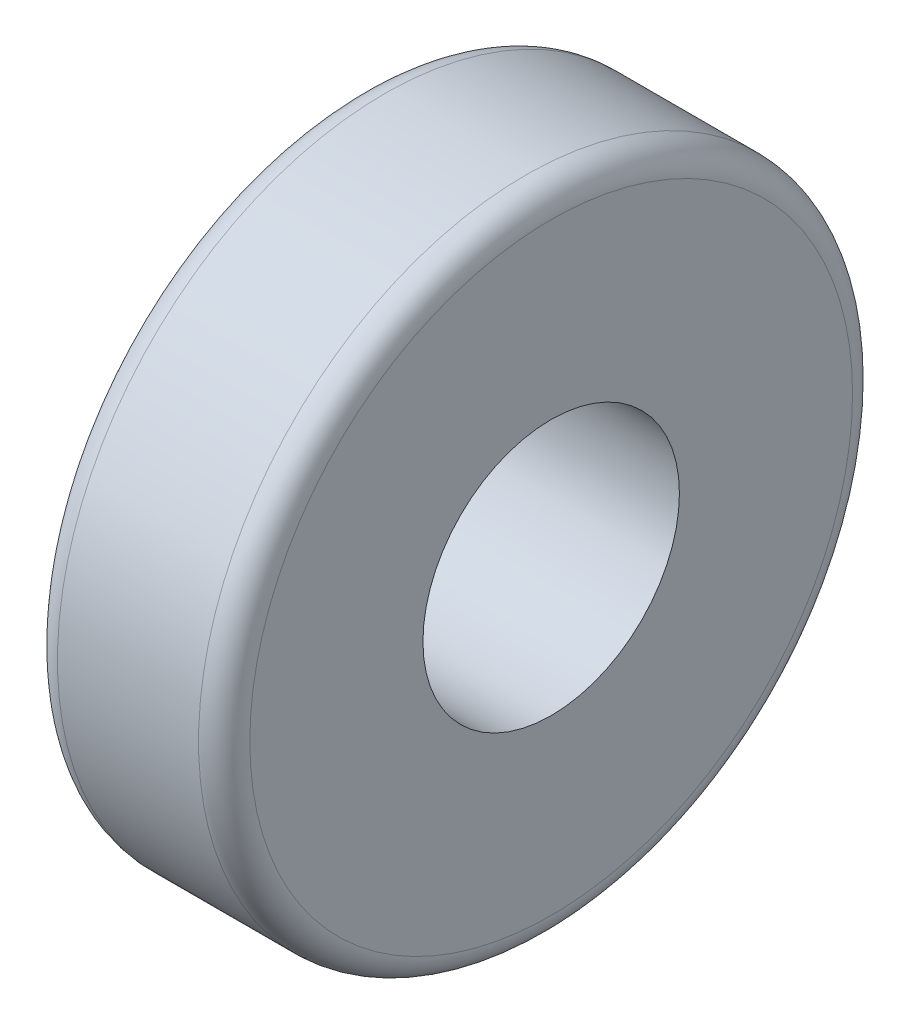
SolidWorks part; units mm, degrees
ref_plane "前视基准面" through (0, 0, 0) normal (0, 0, 1) x (1, 0, 0)
ref_plane "上视基准面" through (0, 0, 0) normal (0, 1, 0) x (1, 0, 0)
ref_plane "右视基准面" through (0, 0, 0) normal (1, 0, 0) x (0, 0, -1)
sketch "草图1" plane through (0, 0, 0) normal (1, 0, 0) x (0, 0, -1)
  circle A0 centre (0, 0) radius 2.55
  circle A1 centre (0, 0) radius 1
  dimension "D1" = 5.1
  dimension "D2" = 2
extrude "凸台-拉伸1" add sketch "草图1" along normal blind 1.5
fillet "圆角1" radius 0.2 2 edges at (1.5, 0, -2.55) (0, 0, -2.55)
